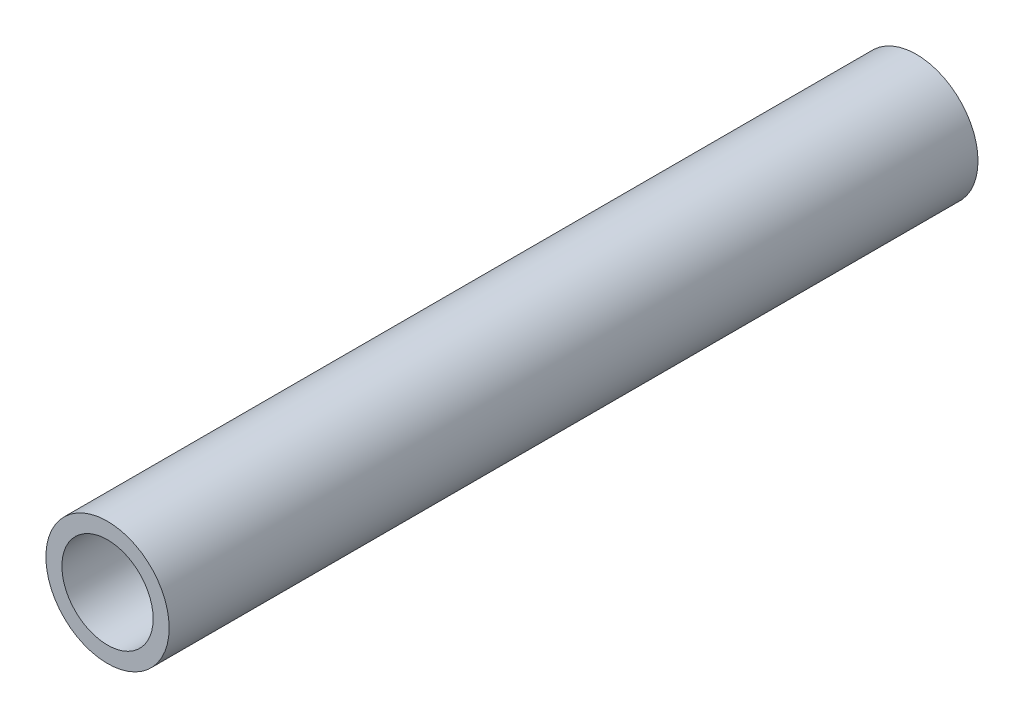
SolidWorks part; units mm, degrees
ref_plane "Front Plane" through (0, 0, 0) normal (0, 0, 1) x (1, 0, 0)
ref_plane "Top Plane" through (0, 0, 0) normal (0, 1, 0) x (1, 0, 0)
ref_plane "Right Plane" through (0, 0, 0) normal (1, 0, 0) x (0, 0, -1)
sketch "Sketch1" plane through (0, 0, 0) normal (0, 0, 1) x (1, 0, 0)
  circle A0 centre (0, 0) radius 10.668
  dimension "Pipe OD" = 21.336
extrude "Extrude-Thin1" add sketch "Sketch1" along normal mid plane 140 thin thin type one direction reverse wall 2.7686
